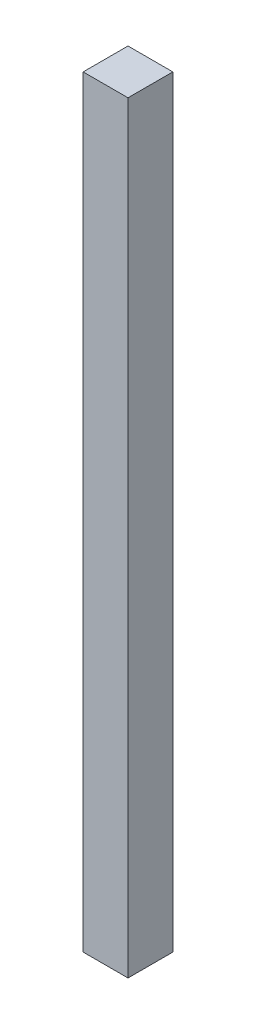
SolidWorks part; units mm, degrees
ref_plane "Front Plane" through (0, 0, 0) normal (0, 0, 1) x (1, 0, 0)
ref_plane "Top Plane" through (0, 0, 0) normal (0, 1, 0) x (1, 0, 0)
ref_plane "Right Plane" through (0, 0, 0) normal (1, 0, 0) x (0, 0, -1)
sketch "Sketch1" plane through (0, 0, 0) normal (0, 0, 1) x (1, 0, 0)
  line L1 (-12.7, -215.9) -> (12.7, -215.9)
  line L2 (-12.7, -215.9) -> (-12.7, 215.9)
  line L3 (-12.7, 215.9) -> (12.7, 215.9)
  line L4 (12.7, -215.9) -> (12.7, 215.9)
  line L5 (-12.7, -215.9) -> (12.7, 215.9) construction
  line L6 (-12.7, 215.9) -> (12.7, -215.9) construction
  point P0 (0, 0)
  dimension "D1" = 431.8
  dimension "D2" = 25.4
extrude "Boss-Extrude1" add sketch "Sketch1" along normal blind 25.4
